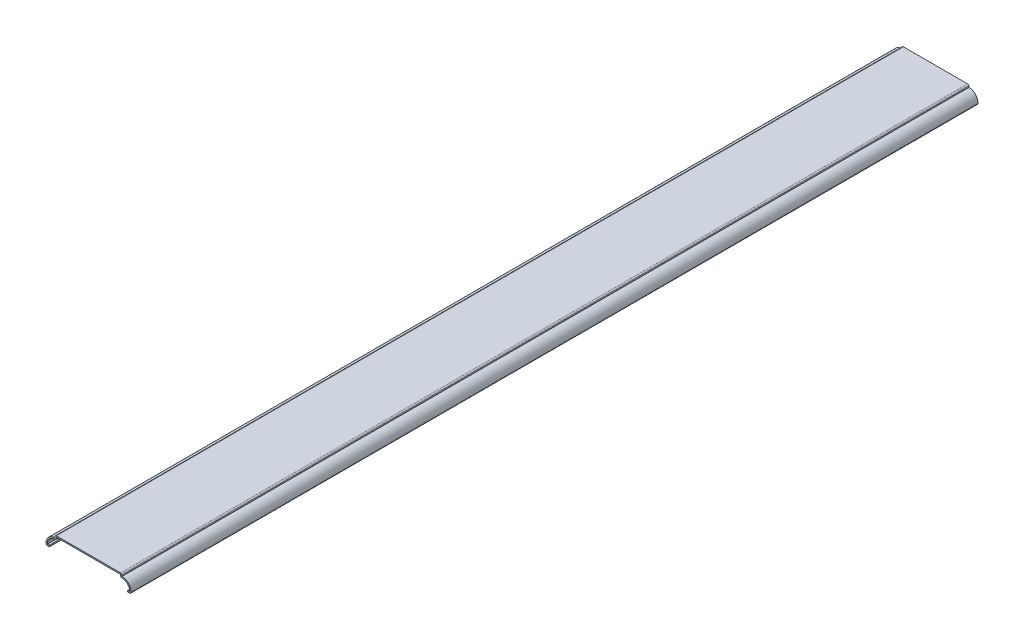
SolidWorks part; units mm, degrees
ref_plane "Front Plane" through (0, 0, 0) normal (0, 0, 1) x (1, 0, 0)
ref_plane "Top Plane" through (0, 0, 0) normal (0, 1, 0) x (1, 0, 0)
ref_plane "Right Plane" through (0, 0, 0) normal (1, 0, 0) x (0, 0, -1)
sketch "Sketch1" plane through (0, 0, 0) normal (0, 0, 1) x (1, 0, 0)
  line L0 (0, 31.7792) -> (0, 0) construction
  line L1 (0, 0) -> (-41.275, 0) construction
  line L2 (-38.1, 0) -> (-41.275, 0)
  line L3 (-32.5437, 10.3187) -> (-32.5437, 12.7)
  line L4 (-32.5437, 12.7) -> (32.5437, 12.7)
  line L5 (32.5437, 10.3187) -> (32.5437, 12.7)
  line L6 (38.1, 0) -> (41.275, 0)
  arc A0 (-41.275, 0) -> (-32.5437, 10.3187) centre (-32.6895, 1.5887) cw
  arc A1 (41.275, 0) -> (32.5437, 10.3187) centre (32.6895, 1.5887) ccw
  point P13 (0, 12.7)
extrude "Extrude-Thin1" add sketch "Sketch1" against normal blind 825.5 thin
fillet "Fillet1" radius 1.27 6 edges at (-41.275, 0, -412.75) (41.275, 0, -412.75) (31.2737, 8.9144, -412.75) (-31.2737, 8.9144, -412.75) (-32.5437, 12.7, -412.75) (32.5437, 12.7, -412.75)
equation "\"D1@Extrude-Thin1\"=\"D1@Sketch1\"*10"
